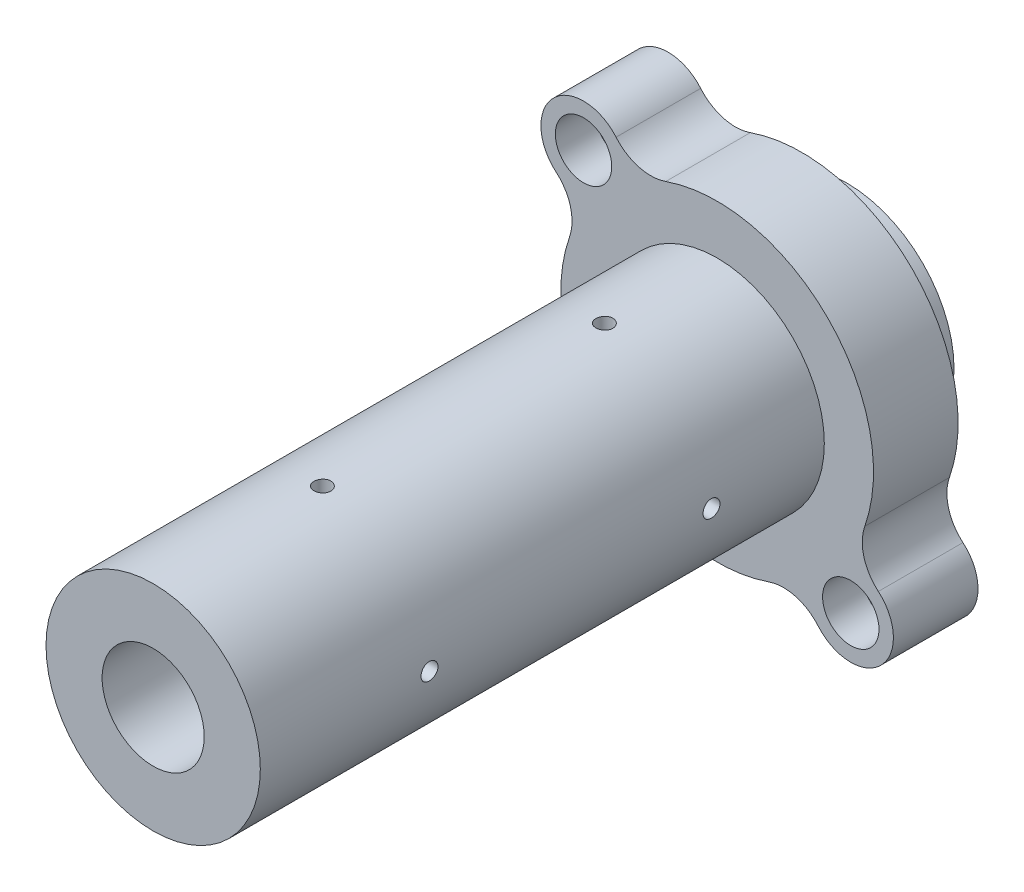
SolidWorks part; units mm, degrees
ref_plane "FRONT" through (0, 0, 0) normal (0, 0, 1) x (1, 0, 0)
ref_plane "TOP" through (0, 0, 0) normal (0, 1, 0) x (1, 0, 0)
ref_plane "RIGHT" through (0, 0, 0) normal (1, 0, 0) x (0, 0, -1)
ref_plane "Plan1" through (0, 0, 838.2) normal (0, 0, 1) x (1, 0, 0)
sketch "Esquisse1" plane through (0, 0, 838.2) normal (0, 0, 1) x (1, 0, 0)
  arc A0 (-9.1186, 26.1774) -> (-17.9219, 28.5774) centre (-11.7713, 33.7926) cw
  arc A1 (-17.9219, 28.5774) -> (-28.5774, 17.9219) centre (-23.6881, 23.6881) ccw
  arc A2 (-28.5774, 17.9219) -> (-26.1774, 9.1186) centre (-33.7926, 11.7713) cw
  arc A3 (-26.1774, 9.1186) -> (9.1186, -26.1774) centre (0, 0) ccw
  arc A4 (9.1186, -26.1774) -> (17.9219, -28.5774) centre (11.7713, -33.7926) cw
  arc A5 (17.9219, -28.5774) -> (28.5774, -17.9219) centre (23.6881, -23.6881) ccw
  arc A6 (28.5774, -17.9219) -> (26.1774, -9.1186) centre (33.7926, -11.7713) cw
  arc A7 (26.1774, -9.1186) -> (-9.1186, 26.1774) centre (0, 0) ccw
  circle A8 centre (23.6881, -23.6881) radius 2.55
  circle A9 centre (-23.6881, 23.6881) radius 2.55
  dimension "D1" = 67
extrude "Boss.-Extru.1" add sketch "Esquisse1" against normal blind 15
sketch "Esquisse9" plane through (0, 0, 838.2) normal (0, 0, 1) x (1, 0, 0)
  circle A0 centre (0, 0) radius 19
extrude "Boss.-Extru.4" add sketch "Esquisse9" along normal blind 100 and the other way blind 23
sketch "Esquisse12" plane through (0, 0, 938.2) normal (0, 0, 1) x (1, 0, 0)
  circle A0 centre (0, 0) radius 9.05
extrude "Enlèv. mat.-Extru.2" cut sketch "Esquisse12" against normal through all
sketch "Esquisse13" plane through (0, 0, 838.2) normal (0, 0, 1) x (1, 0, 0)
  circle A0 centre (-23.6881, 23.6881) radius 5
  circle A1 centre (23.6881, -23.6881) radius 5
extrude "Enlèv. mat.-Extru.3" cut sketch "Esquisse13" against normal blind 7
sketch "Esquisse14" plane through (0, 0, 0) normal (0, 1, 0) x (1, 0, 0)
  line L0 (0, -953.6616) -> (0, -802.1089) construction
  line L1 (-55, -838.2) -> (55, -838.2) construction
  circle A0 centre (0, -858.2) radius 1.5
  circle A1 centre (0, -908.2) radius 1.5
  dimension "D1" = 20
  dimension "D2" = 50
extrude "Enlèv. mat.-Extru.4" cut sketch "Esquisse14" against normal through all both and the other way through all
sketch "Esquisse15" plane through (0, 0, 0) normal (1, 0, 0) x (0, 0, -1)
  line L0 (-972.889, 0) -> (-803.6419, 0) construction
  line L1 (-838.2, 55) -> (-838.2, -55) construction
  circle A0 centre (-858.2, 0) radius 1.5
  circle A1 centre (-908.2, 0) radius 1.5
  dimension "D1" = 20
  dimension "D2" = 50
extrude "Enlèv. mat.-Extru.5" cut sketch "Esquisse15" against normal through all both and the other way through all
